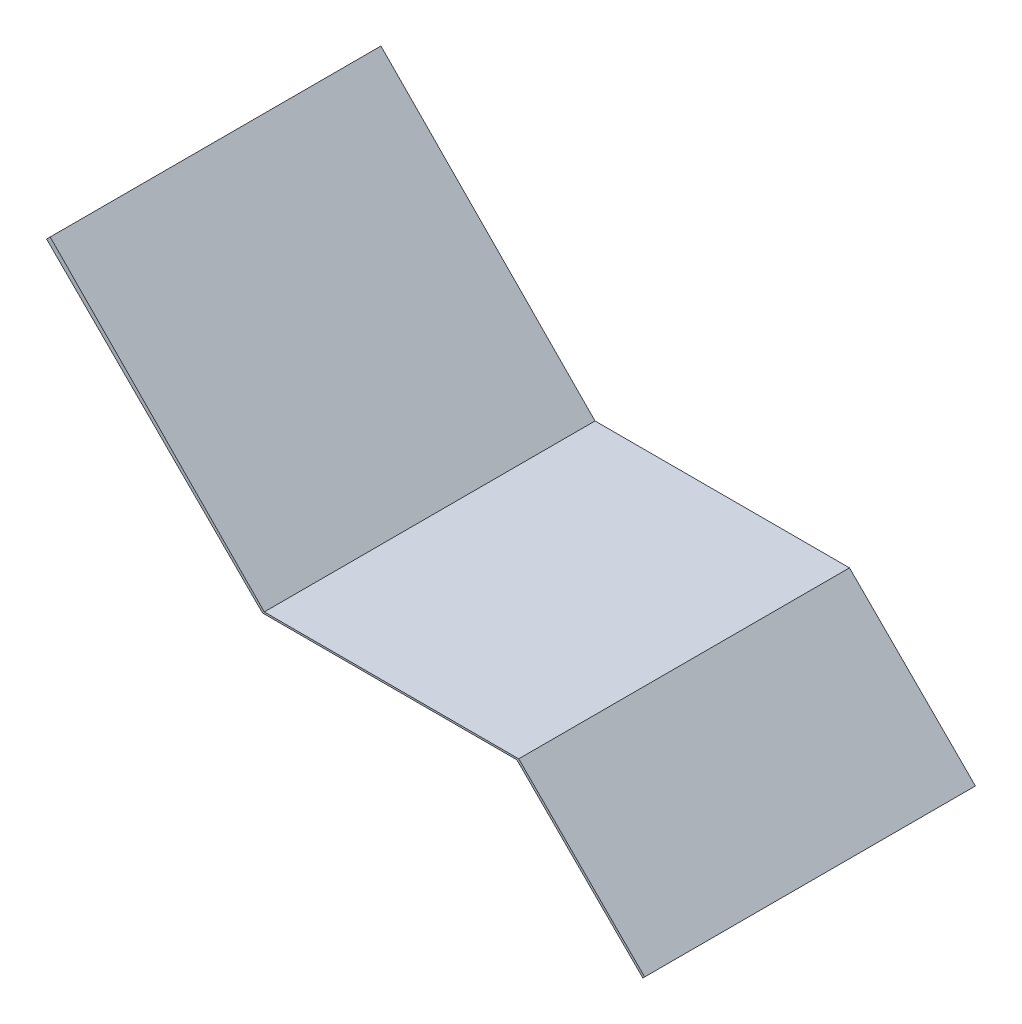
SolidWorks part; units mm, degrees
ref_plane "前视基准面" through (0, 0, 0) normal (0, 0, 1) x (1, 0, 0)
ref_plane "上视基准面" through (0, 0, 0) normal (0, 1, 0) x (1, 0, 0)
ref_plane "右视基准面" through (0, 0, 0) normal (1, 0, 0) x (0, 0, -1)
sketch "草图1" plane through (0, 0, 0) normal (0, 0, 1) x (1, 0, 0)
  line L0 (-66.5116, 45.6766) -> (357.7525, -378.5874)
  line L1 (357.7525, -378.5874) -> (857.7525, -378.5874)
  line L2 (857.7525, -378.5874) -> (1105.2399, -626.0748)
  line L3 (1105.2399, -626.0748) -> (1108.7754, -622.5393)
  line L4 (1108.7754, -622.5393) -> (861.288, -375.0519)
  line L5 (861.288, -375.0519) -> (361.288, -375.0519)
  line L6 (361.288, -375.0519) -> (-59.4654, 52.7228)
  line L7 (-59.4654, 52.7228) -> (-66.5116, 45.6766)
  dimension "D1" = 600
  dimension "D2" = 500
  dimension "D3" = 350
  dimension "D4" = 5
extrude "凸台-拉伸1" add sketch "草图1" along normal blind 650
